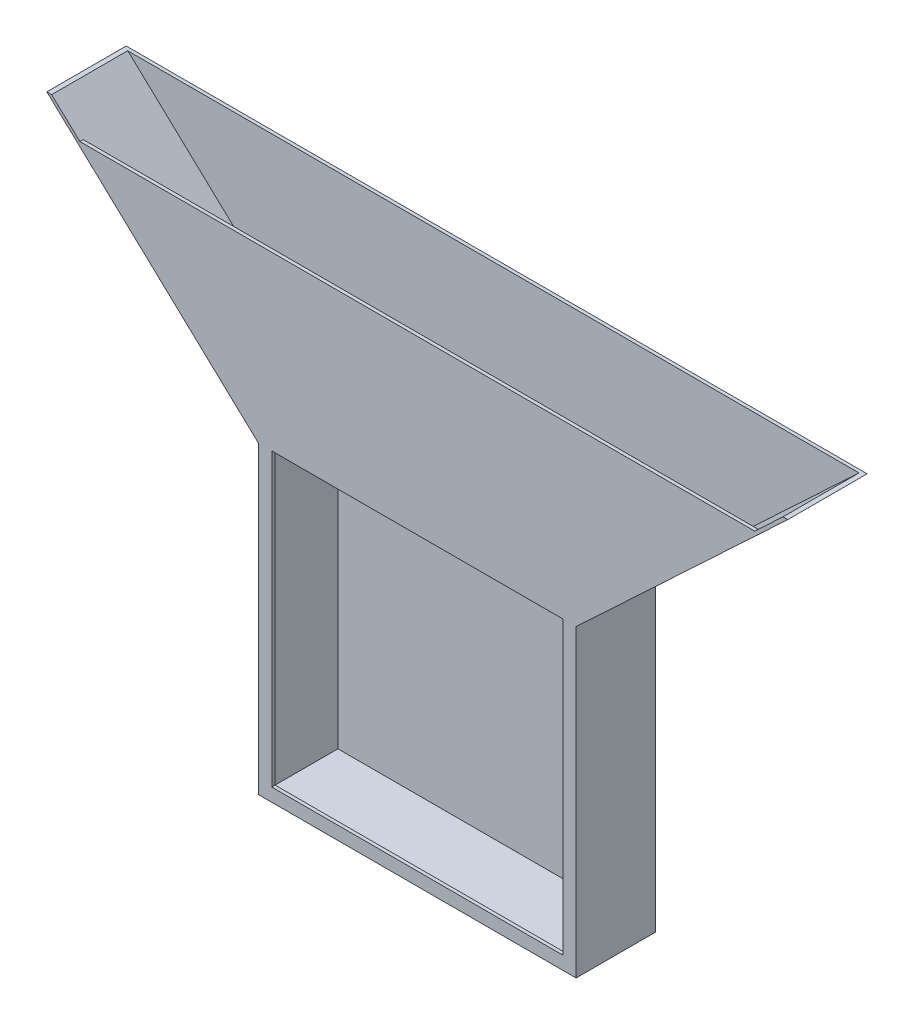
SolidWorks part; units mm, degrees
ref_plane "Front Plane" through (0, 0, 0) normal (0, 0, 1) x (1, 0, 0)
ref_plane "Top Plane" through (0, 0, 0) normal (0, 1, 0) x (1, 0, 0)
ref_plane "Right Plane" through (0, 0, 0) normal (1, 0, 0) x (0, 0, -1)
sketch "Sketch1" plane through (0, 0, 0) normal (0, 0, 1) x (1, 0, 0)
  line L0 (-152.4, 146.05) -> (152.4, -146.05) construction
  line L1 (-152.4, 146.05) -> (152.4, 146.05) construction
  line L2 (-152.4, 146.05) -> (-152.4, -146.05)
  line L3 (-152.4, -146.05) -> (152.4, -146.05)
  line L4 (152.4, 146.05) -> (152.4, -146.05)
  line L5 (-355.6, 336.55) -> (355.6, 336.55)
  line L6 (-355.6, 336.55) -> (-152.4, 146.05)
  line L7 (152.4, 146.05) -> (355.6, 336.55)
  line L8 (0, 336.55) -> (0, -146.05) construction
  dimension "D1" = 292.1
  dimension "D2" = 304.8
  dimension "D3" = 711.2
  dimension "D4" = 190.5
extrude "Boss-Extrude1" add sketch "Sketch1" along normal mid plane 76.2
shell "Shell2" thickness 3.175
sketch "Sketch2" plane through (0, 0, 38.1) normal (0, 0, 1) x (1, 0, 0)
  line L0 (-323.8645, 311.15) -> (323.8645, 311.15)
  line L1 (-139.7, -133.35) -> (139.7, -133.35)
  line L2 (-139.7, -133.35) -> (-139.7, 146.05)
  line L3 (-139.7, 146.05) -> (139.7, 146.05)
  line L4 (139.7, -133.35) -> (139.7, 146.05)
  line L5 (-350.9578, 336.55) -> (-323.8645, 311.15)
  line L6 (355.6, 336.55) -> (-355.6, 336.55) construction
  line L7 (323.8645, 311.15) -> (350.9578, 336.55)
  line L8 (152.4, 146.05) -> (355.6, 336.55) construction
  line L9 (-355.6, 336.55) -> (-152.4, 146.05) construction
  line L10 (-152.4, 146.05) -> (-152.4, -146.05) construction
  line L11 (-139.7, -133.35) -> (-152.4, -133.35) construction
  line L12 (139.7, -133.35) -> (152.4, -133.35) construction
  line L13 (152.4, -146.05) -> (152.4, 146.05) construction
  line L14 (-139.7, -133.35) -> (-139.7, -146.05) construction
  line L15 (-152.4, -146.05) -> (152.4, -146.05) construction
  line M14 (355.6, 336.55) -> (-355.6, 336.55)
  dimension "D1" = 25.4
  dimension "D2" = 12.7
extrude "Cut-Extrude1" cut sketch "Sketch2" against normal blind 73.025 contours L1 L4 L3 L2 | L0 L7 L5 M14
